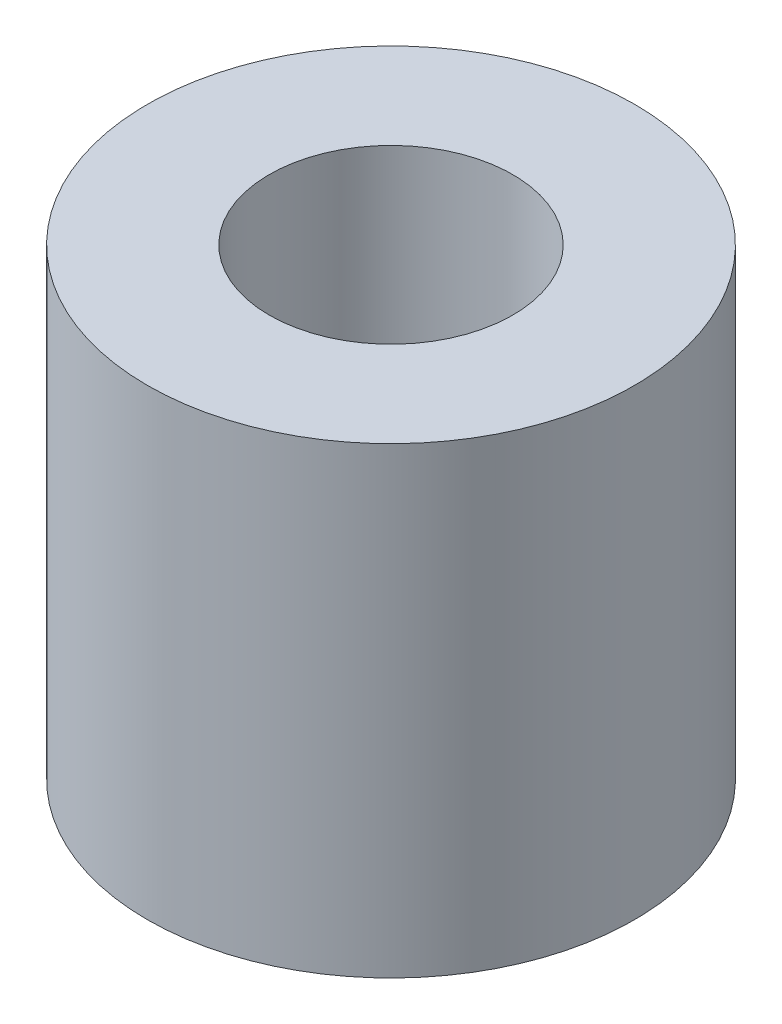
SolidWorks part; units mm, degrees
ref_plane "Front Plane" through (0, 0, 0) normal (0, 0, 1) x (1, 0, 0)
ref_plane "Top Plane" through (0, 0, 0) normal (0, 1, 0) x (1, 0, 0)
ref_plane "Right Plane" through (0, 0, 0) normal (1, 0, 0) x (0, 0, -1)
sketch "Sketch2" plane through (0, 0, 0) normal (0, 1, 0) x (1, 0, 0)
  circle A0 centre (0, 0) radius 2.54
  circle A1 centre (0, 0) radius 5.08
extrude "Boss-Extrude1" add sketch "Sketch2" along normal blind 9.652
